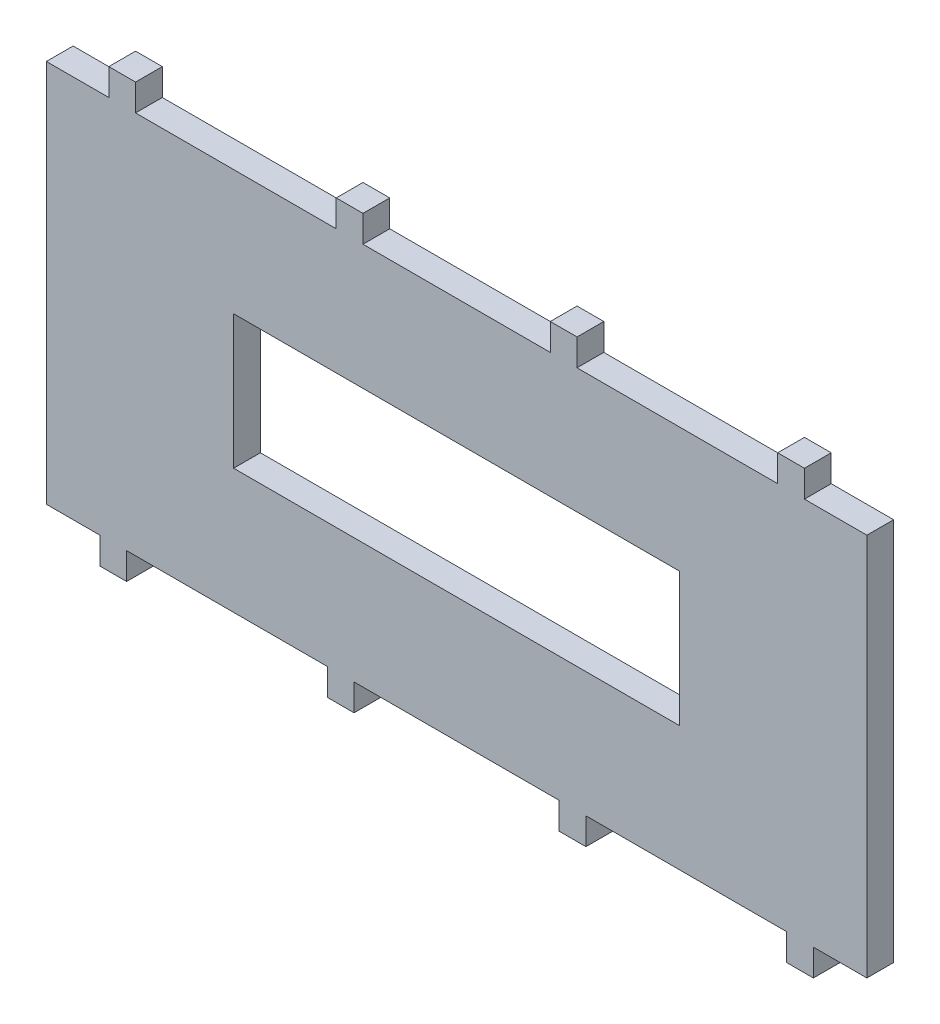
SolidWorks part; units mm, degrees
material "Pine"
ref_plane "정면" through (0, 0, 0) normal (0, 0, 1) x (1, 0, 0)
ref_plane "윗면" through (0, 0, 0) normal (0, 1, 0) x (1, 0, 0)
ref_plane "우측면" through (0, 0, 0) normal (1, 0, 0) x (0, 0, -1)
sketch "Sketch1" plane through (0, 0, 0) normal (0, 0, 1) x (1, 0, 0)
  line L0 (0, -75.4944) -> (0, 77.4838) construction
  line L1 (92, 0) -> (-92, 0)
  line L2 (-92, 0) -> (-92, 86)
  line L3 (-92, 86) -> (92, 86)
  line L4 (92, 0) -> (92, 86)
  point P8 (0, 0)
  point P9 (0, 86)
  dimension "D1" = 92
  dimension "D2" = 86
extrude "Boss-Extrude1" add sketch "Sketch1" along normal blind 6
sketch "Sketch2" plane through (0, 0, 0) normal (0, 0, 1) x (1, 0, 0)
  line L0 (0, 91.2799) -> (0, -43.8398) construction
  line L1 (-80, 0) -> (-80, -6)
  line L2 (-92, 0) -> (92, 0) construction
  line L3 (-80, -6) -> (-74, -6)
  line L4 (-74, -6) -> (-74, 0)
  line L5 (-74, 0) -> (-80, 0)
  line L6 (-92, 86) -> (-92, 0) construction
  line L7 (-29, 0) -> (-29, -6)
  line L8 (-29, -6) -> (-23, -6)
  line L9 (-23, -6) -> (-23, 0)
  line L10 (-23, 0) -> (-29, 0)
  line L11 (23, 0) -> (29, 0)
  line L12 (23, -6) -> (23, 0)
  line L13 (29, -6) -> (23, -6)
  line L14 (29, 0) -> (29, -6)
  line L15 (74, 0) -> (80, 0)
  line L16 (74, -6) -> (74, 0)
  line L17 (80, -6) -> (74, -6)
  line L18 (80, 0) -> (80, -6)
  line L19 (-78, 92) -> (-78, 86)
  line L20 (-78, 86) -> (-72, 86)
  line L21 (-72, 86) -> (-72, 92)
  line L22 (-72, 92) -> (-78, 92)
  line L23 (-27, 92) -> (-27, 86)
  line L24 (-27, 86) -> (-21, 86)
  line L25 (-21, 86) -> (-21, 92)
  line L26 (-21, 92) -> (-27, 92)
  line L27 (21, 92) -> (27, 92)
  line L28 (92, 86) -> (-92, 86) construction
  line L29 (21, 86) -> (21, 92)
  line L30 (27, 86) -> (21, 86)
  line L31 (27, 92) -> (27, 86)
  line L32 (72, 92) -> (78, 92)
  line L33 (72, 86) -> (72, 92)
  line L34 (78, 86) -> (72, 86)
  line L35 (78, 92) -> (78, 86)
  dimension "D1" = 12
  dimension "D2" = 6
  dimension "D3" = 6
  dimension "D4" = 6
  dimension "D5" = 6
  dimension "D6" = 45
  dimension "D7" = 6
  dimension "D8" = 6
  dimension "D9" = 6
  dimension "D10" = 6
  dimension "D11" = 45
  dimension "D12" = 14
extrude "Boss-Extrude2" add sketch "Sketch2" along normal blind 6
sketch "Sketch3" plane through (0, 0, 6) normal (0, 0, 1) x (1, 0, 0)
  line L0 (0, -31.3718) -> (0, 113.4526) construction
  line L1 (50, 28) -> (-50, 28)
  line L2 (-50, 28) -> (-50, 58)
  line L3 (-50, 58) -> (50, 58)
  line L4 (-23, 0) -> (23, 0) construction
  line L6 (50, 28) -> (50, 58)
  point P10 (0, 28)
  point P11 (0, 58)
  dimension "D1" = 50
  dimension "D2" = 30
  dimension "D3" = 28
extrude "Cut-Extrude1" cut sketch "Sketch3" against normal blind 6
